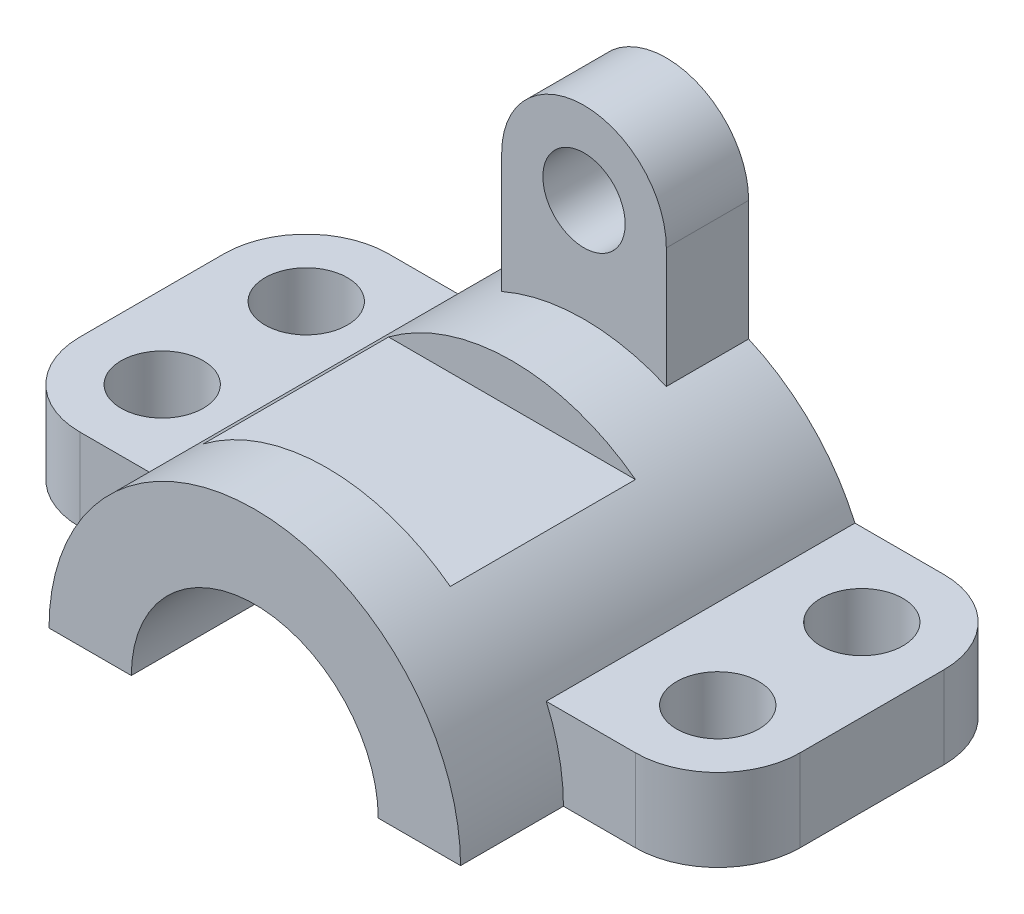
SolidWorks part; units mm, degrees
ref_plane "前视基准面" through (0, 0, 0) normal (0, 0, 1) x (1, 0, 0)
ref_plane "上视基准面" through (0, 0, 0) normal (0, 1, 0) x (1, 0, 0)
ref_plane "右视基准面" through (0, 0, 0) normal (1, 0, 0) x (0, 0, -1)
sketch "草图2" plane through (0, 0, 0) normal (0, 0, 1) x (1, 0, 0)
  line L0 (-40, 0) -> (-24, 0)
  line L1 (24, 0) -> (40, 0)
  arc A0 (24, 0) -> (-24, 0) centre (0, 0) ccw
  arc A1 (40, 0) -> (-40, 0) centre (0, 0) ccw
extrude "凸台-拉伸1" add sketch "草图2" along normal blind 80
sketch "草图3" plane through (0, 0, 0) normal (0, 1, 0) x (1, 0, 0)
  line L0 (32.9517, 0) -> (54, 0)
  line L1 (70, -16) -> (70, -44)
  line L2 (54, -60) -> (32.9517, -60)
  line L4 (32.9517, -60) -> (32.9517, 0)
  line L5 (-32.9517, -60) -> (-32.9517, 0)
  line L6 (-54, -60) -> (-32.9517, -60)
  line L7 (-70, -16) -> (-70, -44)
  line L8 (-32.9517, 0) -> (-54, 0)
  arc A0 (70, -44) -> (54, -60) centre (54, -44) cw
  arc A1 (70, -16) -> (54, 0) centre (54, -16) ccw
  circle A2 centre (54, -16) radius 8
  circle A3 centre (54, -44) radius 8
  circle A4 centre (-54, -44) radius 8
  circle A5 centre (-54, -16) radius 8
  arc A6 (-70, -16) -> (-54, 0) centre (-54, -16) cw
  arc A7 (-70, -44) -> (-54, -60) centre (-54, -44) ccw
extrude "凸台-拉伸2" add sketch "草图3" along normal blind 16
ref_plane "基准面1" through (0, 32, 0) normal (0, 1, 0) x (1, 0, 0)
sketch "草图4" plane through (0, 32, 0) normal (0, 1, 0) x (1, 0, 0)
  line L1 (-41.2842, -30) -> (43.263, -30)
  line L2 (-41.2842, -66) -> (43.263, -66)
  line L3 (-41.2842, -30) -> (-41.2842, -66)
  line L4 (43.263, -30) -> (43.263, -66)
  dimension "D1" = 36
extrude "切除-拉伸1" cut sketch "草图4" along normal blind 33
sketch "草图5" plane through (0, 0, 0) normal (0, 0, 1) x (1, 0, 0)
  line L1 (-16, 60) -> (-16, 36.6606)
  line L2 (16, 60) -> (16, 36.6606)
  line L3 (16, 36.6606) -> (-16, 36.6606)
  circle A0 centre (0, 60) radius 8
  arc A1 (16, 60) -> (-16, 60) centre (0, 60) ccw
  arc A2 (40, 0) -> (-40, 0) centre (0, 0) ccw construction
extrude "凸台-拉伸3" add sketch "草图5" along normal blind 16
